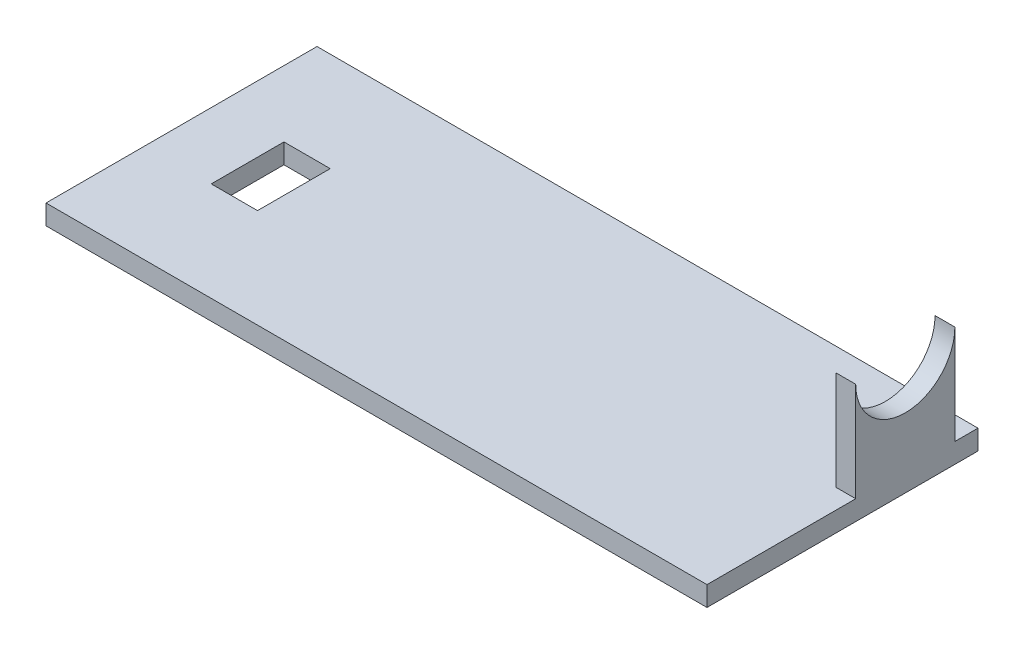
SolidWorks part; units mm, degrees
ref_plane "Plan de face" through (0, 0, 0) normal (0, 0, 1) x (1, 0, 0)
ref_plane "Plan de dessus" through (0, 0, 0) normal (0, 1, 0) x (1, 0, 0)
ref_plane "Plan de droite" through (0, 0, 0) normal (1, 0, 0) x (0, 0, -1)
sketch "Esquisse1" plane through (0, 0, 0) normal (0, 1, 0) x (1, 0, 0)
  line L1 (50, -20.5) -> (-50, -20.5)
  line L2 (50, -20.5) -> (50, 20.5)
  line L3 (50, 20.5) -> (-50, 20.5)
  line L4 (-50, -20.5) -> (-50, 20.5)
  line L5 (50, -20.5) -> (-50, 20.5) construction
  line L6 (50, 20.5) -> (-50, -20.5) construction
  point P0 (0, 0)
  dimension "D1" = 100
  dimension "D2" = 41
extrude "Boss.-Extru.1" add sketch "Esquisse1" along normal blind 3
sketch "Esquisse2" plane through (0, 3, 0) normal (0, 1, 0) x (1, 0, 0)
  line L1 (-40, 5.5) -> (-33, 5.5)
  line L2 (-40, 5.5) -> (-40, -5.5)
  line L3 (-40, -5.5) -> (-33, -5.5)
  line L4 (-33, 5.5) -> (-33, -5.5)
  line L5 (0, 0) -> (-50, 0) construction
  line L6 (-50, 20.5) -> (-50, -20.5) construction
  point P10 (-33, 0)
  dimension "D1" = 11
  dimension "D2" = 7
  dimension "D3" = 10
extrude "Enlèv. mat.-Extru.2" cut sketch "Esquisse2" against normal blind 3
sketch "Esquisse3" plane through (0, 0, 0) normal (0, -1, 0) x (1, 0, 0)
  line L0 (50, 20.5) -> (50, -20.5) construction
  line L1 (50, -17) -> (47, -17)
  line L2 (50, -17) -> (50, -2)
  line L3 (50, -2) -> (47, -2)
  line L4 (47, -17) -> (47, -2)
  line L5 (50, -20.5) -> (-50, -20.5) construction
  dimension "D1" = 3.5
  dimension "D2" = 3
  dimension "D3" = 15
extrude "Boss.-Extru.2" add sketch "Esquisse3" against normal blind 18
sketch "Esquisse4" plane through (50, 0, 0) normal (1, 0, 0) x (0, 0, -1)
  line L0 (17, 18) -> (2, 18) construction
  circle A0 centre (9.5, 18) radius 7.5
  dimension "D1" = 15
extrude "Enlèv. mat.-Extru.3" cut sketch "Esquisse4" against normal blind 6
